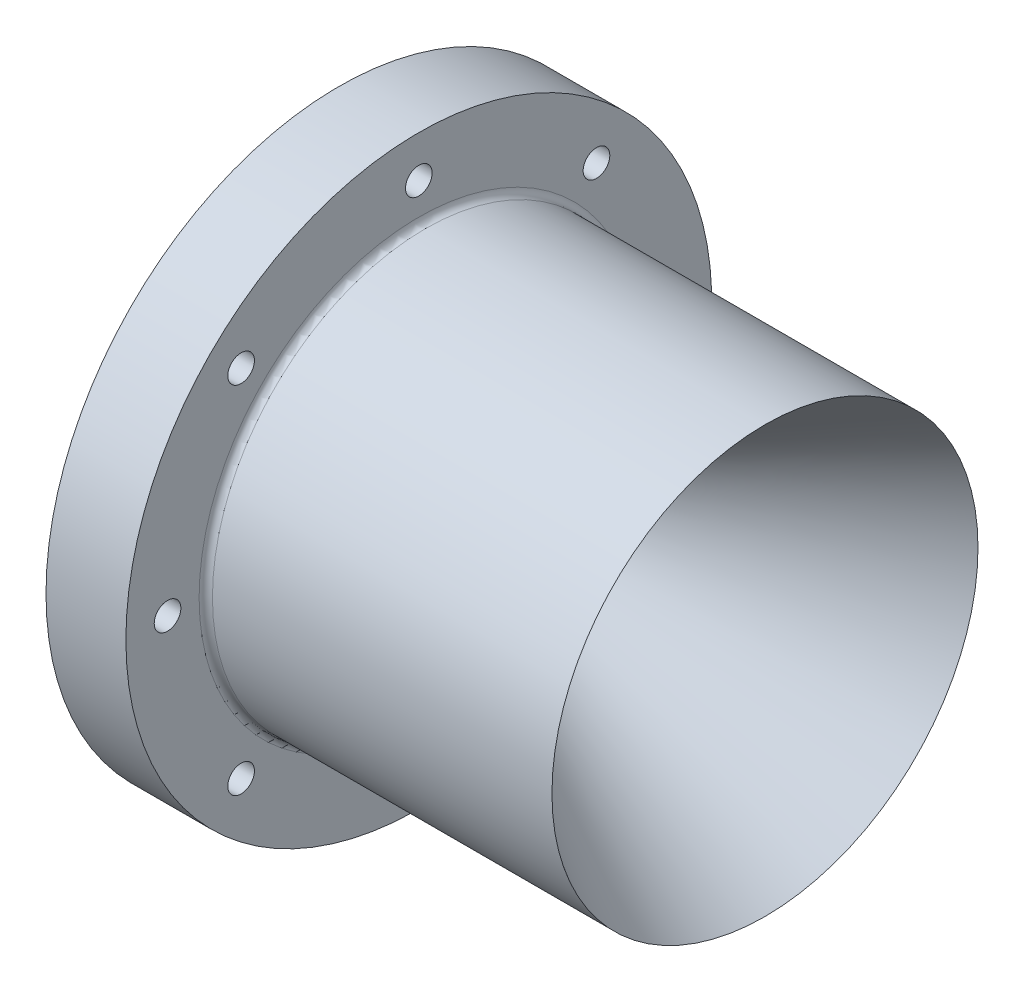
SolidWorks part; units mm, degrees
material "AISI 316 Annealed Stainless Steel Bar (SS)"
ref_plane "Front Plane" through (0, 0, 0) normal (0, 0, 1) x (1, 0, 0)
ref_plane "Top Plane" through (0, 0, 0) normal (0, 1, 0) x (1, 0, 0)
ref_plane "Right Plane" through (0, 0, 0) normal (1, 0, 0) x (0, 0, -1)
sketch "Sketch1" plane through (0, 0, 0) normal (0, 0, 1) x (1, 0, 0)
  line L0 (0, 0) -> (215.3765, 0) construction
  line L1 (0, 0) -> (0, 93.6004) construction
  line L22 (-12.7, 9.525) -> (-30.1096, 39.6793)
  line L23 (-30.1096, 50.8) -> (-30.1096, 39.6793)
  line L24 (-30.1096, 50.8) -> (-30.1096, 69.85)
  line L25 (-30.1096, 69.85) -> (-11.0596, 69.85)
  line L26 (-11.0596, 69.85) -> (-11.0596, 50.8)
  line L29 (71.4904, 50.8) -> (0, 9.525)
  line L30 (71.4904, 50.8) -> (-11.0596, 50.8)
  line L31 (0, 9.525) -> (-12.7, 9.525)
  dimension "D1" = 101.6
  dimension "D2" = 30
  dimension "D3" = 9.525
  dimension "D4" = 19.05
  dimension "D5" = 60
  dimension "D6" = 19.05
  dimension "D7" = 12.7
  dimension "D8" = 69.85
revolve "Revolve1" add sketch "Sketch1" angle 360 about L0
sketch "Sketch3" plane through (-30.1096, 0, 0) normal (-1, 0, 0) x (0, 0, 1)
  circle A0 centre (0, 59.9186) radius 3.175
  circle A1 centre (42.3688, 42.3688) radius 3.175
  circle A2 centre (59.9186, 0) radius 3.175
  circle A3 centre (42.3688, -42.3688) radius 3.175
  circle A4 centre (0, -59.9186) radius 3.175
  circle A5 centre (-42.3688, -42.3688) radius 3.175
  circle A6 centre (-59.9186, 0) radius 3.175
  circle A7 centre (-42.3688, 42.3688) radius 3.175
  point P36 (0, 0)
  dimension "D1" = 6.35
  dimension "D2" = 59.9186
  dimension "D3" = 8
extrude "Cut-Extrude2" cut sketch "Sketch3" against normal up to next
fillet "Fillet1" radius 3.175 2 edges at (-12.7, 0, 9.525) (0, 0, 9.525)
fillet "Fillet2" radius 1.5875 1 edges at (-11.0596, 0, 50.8)
